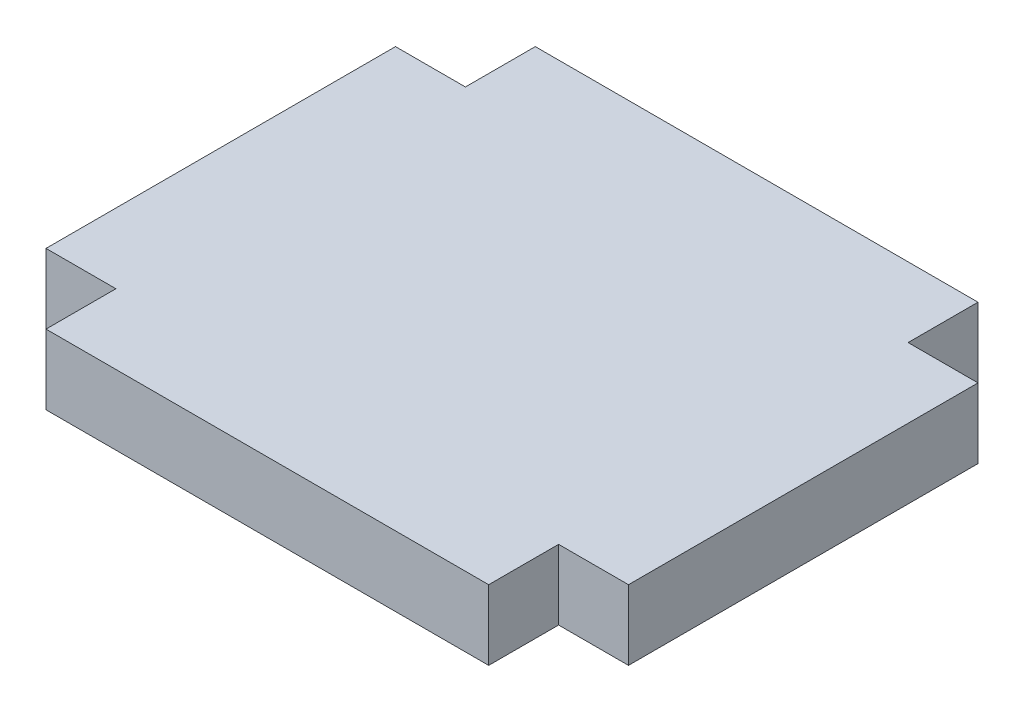
SolidWorks part; units mm, degrees
ref_plane "Front Plane" through (0, 0, 0) normal (0, 0, 1) x (1, 0, 0)
ref_plane "Top Plane" through (0, 0, 0) normal (0, 1, 0) x (1, 0, 0)
ref_plane "Right Plane" through (0, 0, 0) normal (1, 0, 0) x (0, 0, -1)
sketch "Sketch1" plane through (0, 0, 0) normal (0, 1, 0) x (1, 0, 0)
  line L0 (-9.5, 10.5) -> (9.5, 10.5)
  line L1 (9.5, 10.5) -> (9.5, 7.5)
  line L2 (9.5, 7.5) -> (12.5, 7.5)
  line L3 (12.5, 7.5) -> (12.5, -7.5)
  line L4 (12.5, -7.5) -> (9.5, -7.5)
  line L5 (9.5, -7.5) -> (9.5, -10.5)
  line L6 (9.5, -10.5) -> (-9.5, -10.5)
  line L7 (-9.5, -10.5) -> (-9.5, -7.5)
  line L8 (-9.5, -7.5) -> (-12.5, -7.5)
  line L9 (-12.5, -7.5) -> (-12.5, 7.5)
  line L10 (-12.5, 7.5) -> (-9.5, 7.5)
  line L11 (-9.5, 7.5) -> (-9.5, 10.5)
  point P2 (-12.5, 0)
  point P13 (0, 10.5)
  dimension "D1" = 19
  dimension "D2" = 3
  dimension "D3" = 15
extrude "Boss-Extrude1" add sketch "Sketch1" along normal mid plane 3
